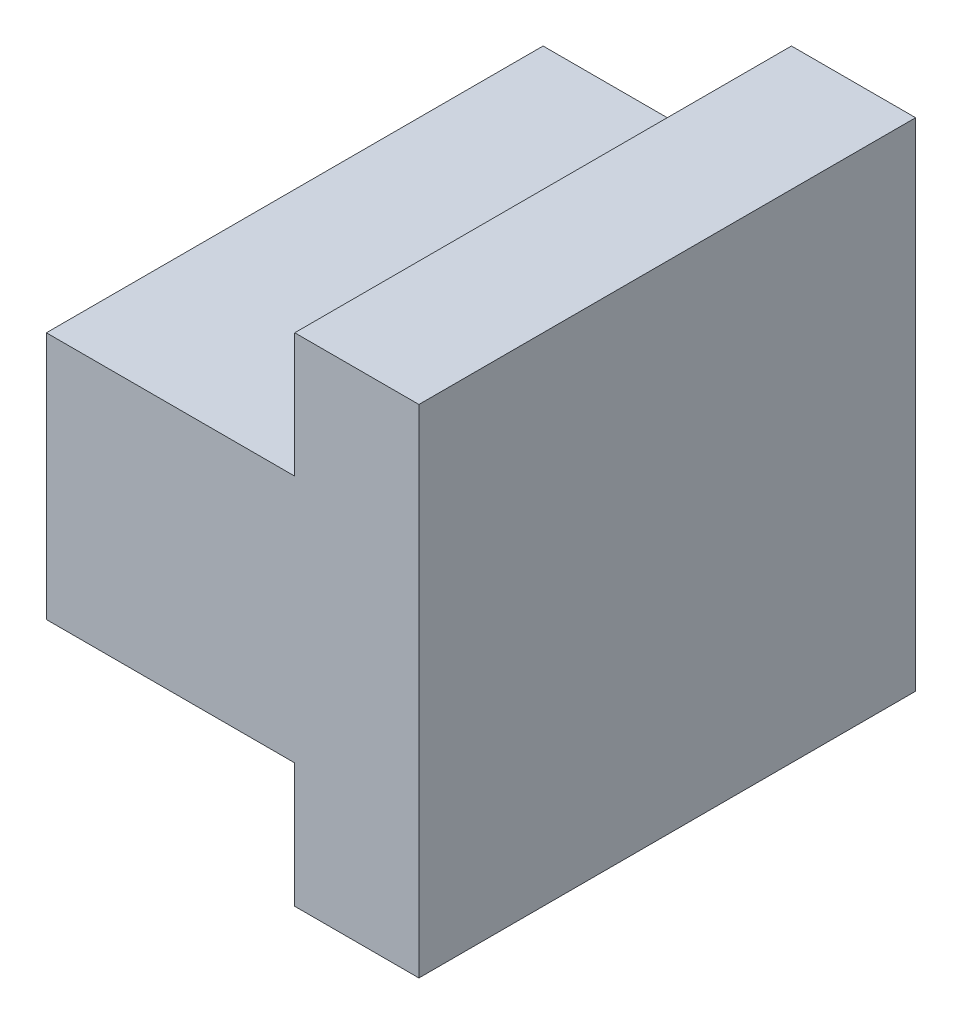
SolidWorks part; units mm, degrees
ref_plane "Front" through (0, 0, 0) normal (0, 0, 1) x (1, 0, 0)
ref_plane "Top" through (0, 0, 0) normal (0, 1, 0) x (1, 0, 0)
ref_plane "Right" through (0, 0, 0) normal (1, 0, 0) x (0, 0, -1)
sketch "Sketch1" plane through (0, 0, 0) normal (0, 0, 1) x (1, 0, 0)
  line L0 (0, 0) -> (0, 2)
  line L1 (0, 2) -> (1, 2)
  line L2 (1, 2) -> (1, 3)
  line L3 (1, 3) -> (3, 3)
  line L4 (3, 3) -> (3, 4)
  line L5 (3, 4) -> (4, 4)
  line L6 (4, 4) -> (4, 0)
  line L7 (4, 0) -> (3, 0)
  line L8 (3, 0) -> (3, 1)
  line L9 (3, 1) -> (1, 1)
  line L10 (1, 1) -> (1, 0)
  line L11 (1, 0) -> (0, 0)
  dimension "D1" = 4
  dimension "D2" = 1
  dimension "D3" = 1
  dimension "D4" = 1
  dimension "D5" = 1
  dimension "D6" = 2
  dimension "D7" = 1
  dimension "D8" = 1
  dimension "D9" = 2
extrude "Boss-Extrude1" add sketch "Sketch1" along normal blind 4
sketch "Sketch2" plane through (0, 0, 4) normal (0, 0, 1) x (1, 0, 0)
  line L5 (1, 3) -> (0, 3)
  line L6 (1, 3) -> (1, 0)
  line L7 (1, 0) -> (0, 0)
  line L8 (0, 3) -> (0, 0)
extrude "Cut-Extrude1" cut sketch "Sketch2" against normal blind 1
